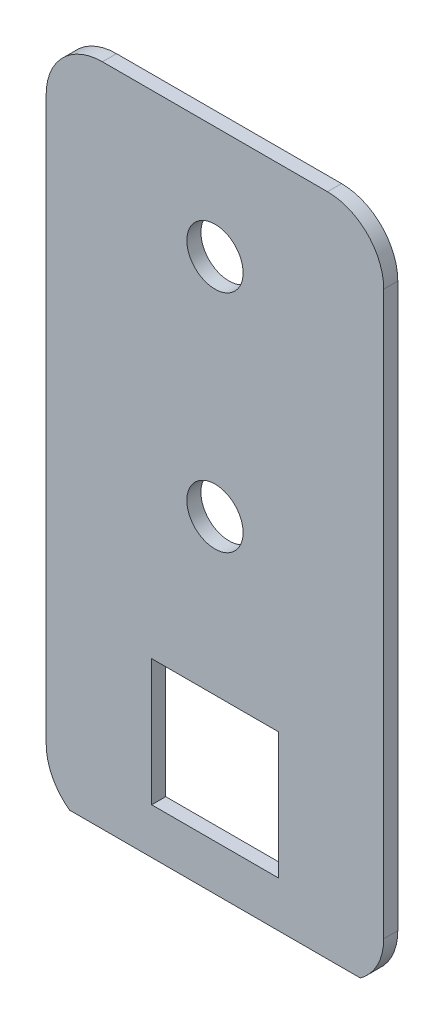
SolidWorks part; units mm, degrees
ref_plane "Front Plane" through (0, 0, 0) normal (0, 0, 1) x (1, 0, 0)
ref_plane "Top Plane" through (0, 0, 0) normal (0, 1, 0) x (1, 0, 0)
ref_plane "Right Plane" through (0, 0, 0) normal (1, 0, 0) x (0, 0, -1)
sketch "Sketch1" plane through (0, 0, 0) normal (0, 0, 1) x (1, 0, 0)
  line L0 (19.05, 0) -> (19.05, 76.2) construction
  line L1 (6.35, 0) -> (31.75, 0)
  line L2 (0, 6.35) -> (0, 69.85)
  line L3 (6.35, 76.2) -> (31.75, 76.2)
  line L4 (38.1, 6.35) -> (38.1, 69.85)
  line L5 (11.9062, 6.35) -> (26.1938, 6.35)
  line L6 (11.9062, 6.35) -> (11.9062, 20.6375)
  line L7 (11.9062, 20.6375) -> (26.1938, 20.6375)
  line L8 (26.1938, 6.35) -> (26.1938, 20.6375)
  circle A0 centre (19.05, 38.1) radius 3.175
  circle A1 centre (19.05, 63.5) radius 3.175
  arc A2 (0, 69.85) -> (6.35, 76.2) centre (6.35, 69.85) cw
  arc A3 (31.75, 76.2) -> (38.1, 69.85) centre (31.75, 69.85) cw
  arc A4 (31.75, 0) -> (38.1, 6.35) centre (31.75, 6.35) ccw
  arc A5 (6.35, 0) -> (0, 6.35) centre (6.35, 6.35) cw
  point P17 (0, 76.2)
  point P20 (38.1, 76.2)
  point P25 (0, 0)
  dimension "D7" = 6.35
  dimension "D8" = 6.35
  dimension "D11" = 6.35
  dimension "D1" = 76.2
  dimension "D2" = 38.1
  dimension "D3" = 14.2875
  dimension "D4" = 6.35
  dimension "D5" = 11.9062
  dimension "D6" = 14.2875
  dimension "D9" = 38.1
  dimension "D10" = 25.4
extrude "Boss-Extrude1" add sketch "Sketch1" along normal blind 1.5875
sketch "Sketch3" plane through (0, 0, 0) normal (-1, 0, 0) x (0, 0, 1)
  line L5 (0.3969, 0) -> (1.5875, 1.1906)
  line L6 (1.5875, 0) -> (1.5875, 6.35) construction
  line L7 (1.5875, 1.1906) -> (1.5875, 0)
  line L8 (1.5875, 0) -> (0, 0) construction
  line L9 (1.5875, 0) -> (0.3969, 0)
  dimension "D1" = 0.3969
  dimension "D2" = 135
extrude "Cut-Extrude1" cut sketch "Sketch3" against normal blind 76.2
